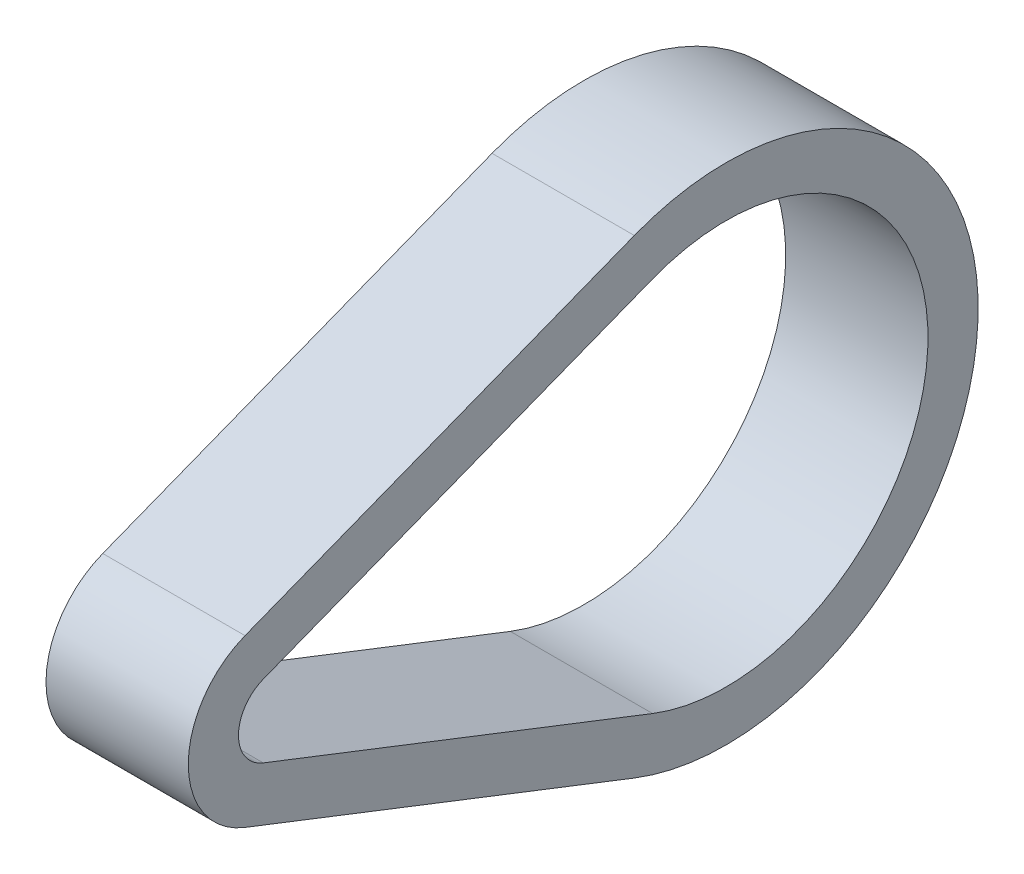
SolidWorks part; units mm, degrees
ref_plane "Front Plane" through (0, 0, 0) normal (0, 0, 1) x (1, 0, 0)
ref_plane "Top Plane" through (0, 0, 0) normal (0, 1, 0) x (1, 0, 0)
ref_plane "Right Plane" through (0, 0, 0) normal (1, 0, 0) x (0, 0, -1)
other "Bounding Box"
ref_plane "Default Plane" through (-8.9266, -12.7485, 0) normal (-0.1736, 0.9848, 0) x (0.9848, 0.1736, 0)
sketch "Sketch1" plane through (0, 0, 0) normal (1, 0, 0) x (0, 0, -1)
  line L0 (0, 0) -> (28.3718, 0) construction
  line L1 (-0.8955, 2.2953) -> (23.728, 11.9024)
  line L2 (-0.8955, -2.2953) -> (23.728, -11.9024)
  line L3 (-2.0496, 5.2531) -> (22.574, 14.8602)
  line L4 (-2.0496, -5.2531) -> (22.574, -14.8602)
  arc A0 (-0.8955, 2.2953) -> (-0.8955, -2.2953) centre (0, 0) ccw
  arc A1 (23.728, -11.9024) -> (23.728, 11.9024) centre (28.3718, 0) ccw
  arc A2 (-2.0496, 5.2531) -> (-2.0496, -5.2531) centre (0, 0) ccw
  arc A3 (22.574, -14.8602) -> (22.574, 14.8602) centre (28.3718, 0) ccw
  dimension "D2" = 3.175
  dimension "D3" = 3.175
  dimension "D4" = 4.9276
  dimension "D5" = 25.5524
  dimension "D1" = 28.3718
extrude "Boss-Extrude1" add sketch "Sketch1" along normal mid plane 9
